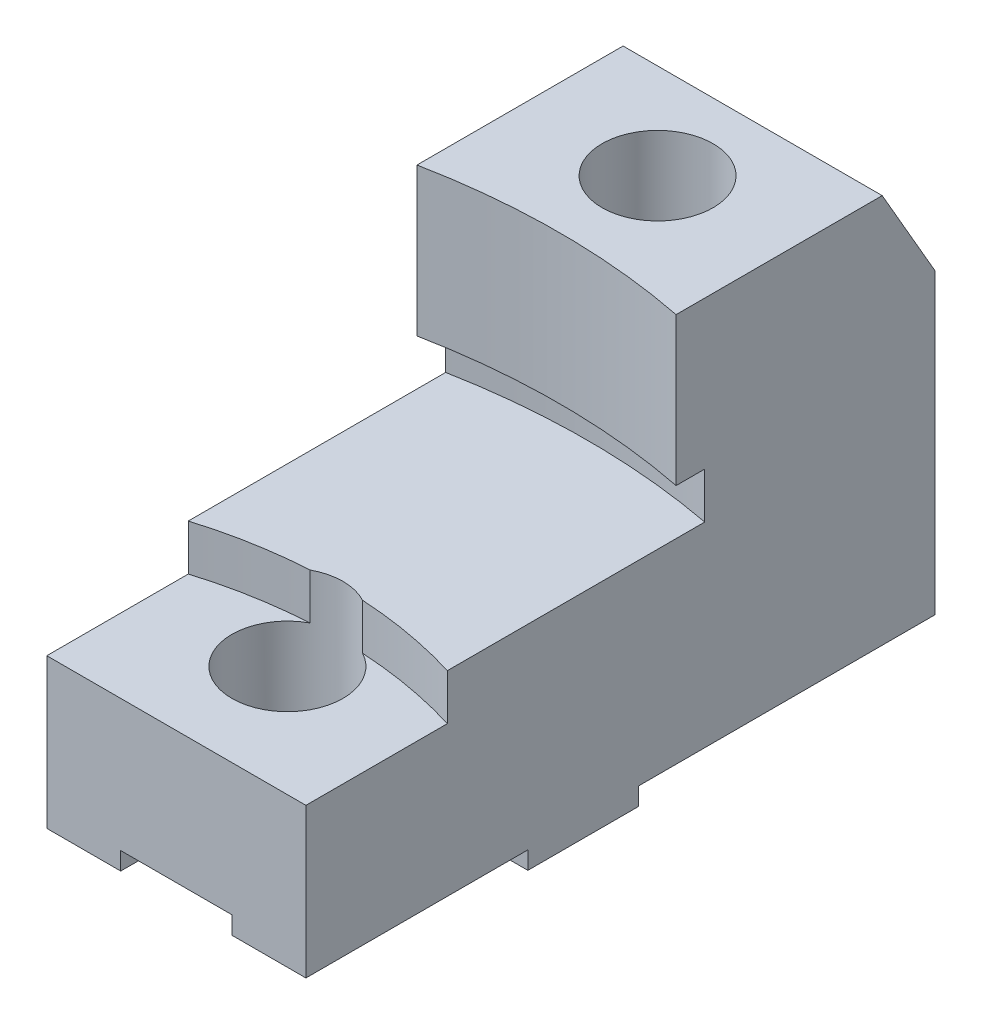
SolidWorks part; units mm, degrees
ref_plane "Frontal" through (0, 0, 0) normal (0, 0, 1) x (1, 0, 0)
ref_plane "Horizontal" through (0, 0, 0) normal (0, 1, 0) x (1, 0, 0)
ref_plane "Profile" through (0, 0, 0) normal (1, 0, 0) x (0, 0, -1)
sketch "Sketch1" plane through (0, 0, 0) normal (0, 1, 0) x (1, 0, 0)
  line L1 (-1.462, 2.1722) -> (0.288, 2.1722)
  line L2 (-1.462, 2.1722) -> (-1.462, -2.0778)
  line L3 (-1.462, -2.0778) -> (0.288, -2.0778)
  line L4 (0.288, 2.1722) -> (0.288, -2.0778)
  dimension "D1" = 1.75
  dimension "D2" = 4.25
extrude "Extrude1" add sketch "Sketch1" along normal blind 2.75
ref_plane "Plane1" through (-1.462, 0, -2.1722) normal (0, -1, 0) x (1, 0, 0)
sketch "Sketch3" plane through (-1.462, 0, 0) normal (-1, 0, 0) x (0, 0, 1)
  line L0 (-2.1722, 2.75) -> (-2.1722, 0) construction
  line L1 (-2.1722, 0.12) -> (-0.1697, 0.12)
  line L2 (-2.1722, 0.12) -> (-2.1722, 0)
  line L3 (-2.1722, 0) -> (-0.1697, 0)
  line L4 (-0.1697, 0.12) -> (-0.1697, 0)
  line L5 (-2.1722, 0) -> (2.0778, 0) construction
  dimension "D1" = 0.12
  dimension "D2" = 2.0025
extrude "Cut-Extrude1" cut sketch "Sketch3" against normal blind 2.75
sketch "Sketch4" plane through (-1.462, 0, 0) normal (-1, 0, 0) x (0, 0, 1)
  line L1 (0.5788, 0.12) -> (2.0778, 0.12)
  line L2 (0.5788, 0.12) -> (0.5788, 0)
  line L3 (0.5788, 0) -> (2.0778, 0)
  line L4 (2.0778, 0.12) -> (2.0778, 0)
  dimension "D1" = 0.12
  dimension "D2" = 1.499
extrude "Cut-Extrude2" cut sketch "Sketch4" against normal blind 2.75
sketch "Sketch5" plane through (0, 0, 2.0778) normal (0, 0, 1) x (1, 0, 0)
  line L0 (0.288, 0) -> (-1.462, 0) construction
  line L1 (-0.9628, 0.24) -> (-0.2113, 0.24)
  line L2 (-0.9628, 0.24) -> (-0.9628, 0)
  line L3 (-0.9628, 0) -> (-0.2113, 0)
  line L4 (-0.2113, 0.24) -> (-0.2113, 0)
  line L5 (-0.587, 2.75) -> (-0.587, -0.1414) construction
  line L6 (-1.462, 2.75) -> (0.288, 2.75) construction
  point P6 (-0.587, 0)
  dimension "D1" = 0.24
  dimension "D2" = 0.7515
extrude "Cut-Extrude3" cut sketch "Sketch5" against normal through all
sketch "Sketch6" plane through (0, 2.75, 0) normal (0, 1, 0) x (-1, 0, 0)
  line L0 (1.462, -2.1722) -> (1.462, 2.0778) construction
  line L1 (-0.288, 2.0778) -> (-0.288, -2.1722) construction
  arc A0 (1.462, -0.4222) -> (-0.288, -0.4222) centre (0.587, 3.9919) cw
  line M2 (1.462, -2.1722) -> (1.462, 2.0778)
  line M3 (1.462, 2.0778) -> (-0.288, 2.0778)
  line M4 (-0.288, 2.0778) -> (-0.288, -2.1722)
  dimension "D1" = 4.5
  dimension "D2" = 1.75
extrude "Cut-Extrude4" cut sketch "Sketch6" against normal blind 1.31 contours A0 M4 M2 M3
sketch "Sketch7" plane through (0, 2.75, 0) normal (0, 1, 0) x (-1, 0, 0)
  line L0 (1.462, -2.1722) -> (1.462, -0.4222) construction
  line L1 (-0.288, -0.4222) -> (-0.288, -2.1722) construction
  line L2 (-0.288, -2.1722) -> (1.462, -2.1722) construction
  line L3 (0.587, -2.1722) -> (0.587, 2.2201) construction
  line L4 (1.462, -0.6157) -> (1.462, -0.4222)
  line L5 (-0.288, -0.6157) -> (-0.288, -0.4222)
  arc A0 (1.462, -0.6157) -> (-0.288, -0.6157) centre (0.587, 3.9919) cw
  arc A1 (-0.288, -0.4222) -> (1.462, -0.4222) centre (0.587, 3.9919) ccw construction
  arc A2 (1.462, -0.4222) -> (-0.288, -0.4222) centre (0.587, 3.9919) cw
  point P11 (0.587, -0.6981)
  point P12 (0.587, -0.5081)
  dimension "D1" = 4.69
  dimension "D2" = 0.19
extrude "Cut-Extrude7" cut sketch "Sketch7" against normal blind 0.31 from offset 1
sketch "Sketch8" plane through (0, 1.44, 0) normal (0, 1, 0) x (-1, 0, 0)
  line L0 (1.462, 2.0778) -> (1.462, -0.6157) construction
  line L1 (-0.288, -0.6157) -> (-0.288, 2.0778) construction
  line L2 (1.462, 1.1224) -> (1.462, 2.0778)
  line L3 (1.462, 2.0778) -> (-0.288, 2.0778)
  line L4 (-0.288, 2.0778) -> (-0.288, 1.1224)
  arc A0 (1.462, 1.1224) -> (-0.288, 1.1224) centre (0.587, 3.9919) cw
  arc A2 (1.462, -0.4222) -> (-0.288, -0.4222) centre (0.587, 3.9919) cw
  point P10 (0.587, 0.9919)
  point P11 (0.587, -0.5081)
  line M1 (-0.288, 2.0778) -> (-0.288, -0.6157)
  line M3 (1.462, -0.6157) -> (1.462, 2.0778)
  line M4 (1.462, 2.0778) -> (-0.288, 2.0778)
  dimension "D1" = 3
  dimension "D2" = 1.5
extrude "Cut-Extrude8" cut sketch "Sketch8" against normal blind 0.31 contours A0 M3 M4 M1
sketch "Sketch11" plane through (0, 1.13, 0) normal (0, 1, 0) x (-1, 0, 0)
  line L0 (0.587, -2.1722) -> (0.587, 2.2201) construction
  line L1 (-0.288, 2.0778) -> (1.462, 2.0778) construction
  circle A0 centre (0.587, 1.3278) radius 0.375
  dimension "D1" = 0.75
extrude "Cut-Extrude10" cut sketch "Sketch11" against normal blind 0.81 and the other way through all
sketch "Sketch13" plane through (0, 0.32, 0) normal (0, 1, 0) x (-1, 0, 0)
  circle A0 centre (0.587, 1.3278) radius 0.25
extrude "Cut-Extrude11" cut sketch "Sketch13" against normal blind 0.81
sketch "Sketch14" plane through (0, 2.75, 0) normal (0, 1, 0) x (-1, 0, 0)
  line L0 (0.587, -2.1722) -> (0.587, 2.2201) construction
  circle A0 centre (0.587, -1.1722) radius 0.375
  circle A1 centre (0.587, 1.3278) radius 0.25
  dimension "D1" = 2.5
  dimension "D2" = 0.75
extrude "Cut-Extrude12" cut sketch "Sketch14" against normal blind 0.81
sketch "Sketch15" plane through (0, 1.94, 0) normal (0, 1, 0) x (-1, 0, 0)
  circle A0 centre (0.587, -1.1722) radius 0.25
extrude "Cut-Extrude13" cut sketch "Sketch15" against normal through all
sketch "Sketch16" plane through (-1.462, 0, 0) normal (-1, 0, 0) x (0, 0, 1)
  line L0 (-2.1722, 2.13) -> (-1.8142, 2.75)
  line L1 (-2.1722, 2.75) -> (-2.1722, 0.12) construction
  line L2 (-2.1722, 2.75) -> (2.2201, 2.75) construction
  line M7 (-0.4222, 2.75) -> (-2.1722, 2.75)
  line M8 (-2.1722, 2.75) -> (-2.1722, 0.12)
  dimension "D1" = 0.62
  dimension "D2" = 30
extrude "Cut-Extrude14" cut sketch "Sketch16" against normal through all contours L0 M8 M7
